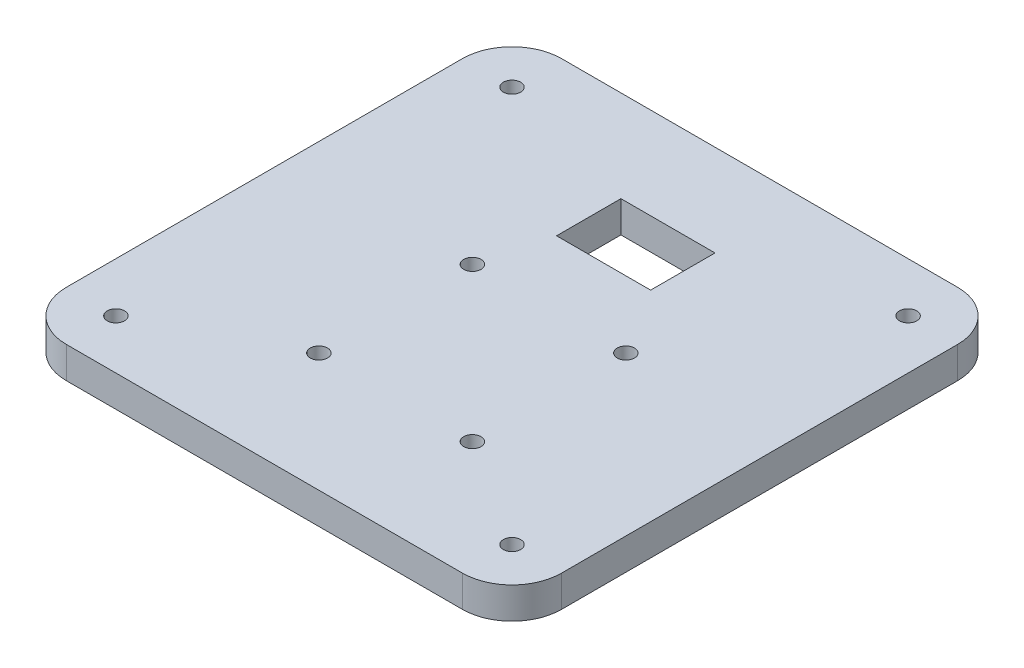
SolidWorks part; units mm, degrees
ref_plane "Front Plane" through (0, 0, 0) normal (0, 0, 1) x (1, 0, 0)
ref_plane "Top Plane" through (0, 0, 0) normal (0, 1, 0) x (1, 0, 0)
ref_plane "Right Plane" through (0, 0, 0) normal (1, 0, 0) x (0, 0, -1)
sketch "Sketch2" plane through (0, 0, 0) normal (0, 1, 0) x (1, 0, 0)
  line L1 (-50, 50) -> (50, 50)
  line L2 (-50, 50) -> (-50, -50)
  line L3 (-50, -50) -> (50, -50)
  line L4 (50, 50) -> (50, -50)
  line L5 (-50, 50) -> (50, -50) construction
  line L6 (-50, -50) -> (50, 50) construction
  point P0 (0, 0)
  dimension "D1" = 100
  dimension "D2" = 100
extrude "Boss-Extrude1" add sketch "Sketch2" along normal blind 6.35 contours L2 L3 L4 L1
sketch "Sketch3" plane through (0, 0, 0) normal (0, -1, 0) x (1, 0, 0)
  line L0 (-50, -50) -> (-50, 50) construction
  line L1 (-50, -50) -> (50, -50) construction
  circle A0 centre (-40, -40) radius 1.75
  dimension "D1" = 10
  dimension "D3" = 3.5
  dimension "D2" = 10
extrude "Cut-Extrude1" cut sketch "Sketch3" against normal through all
pattern_linear "LPattern1" count 2 spacing 80 along (0, 0, 1) of "Cut-Extrude1"
pattern_linear "LPattern2" count 2 spacing 80 along (1, 0, 0) of "LPattern1", "Cut-Extrude1"
sketch "Sketch8" plane through (0, 0, 0) normal (0, -1, 0) x (1, 0, 0)
  line L0 (50, -50) -> (50, 50) construction
  line L1 (-50, -50) -> (50, -50) construction
  circle A0 centre (18, -5) radius 1.75
  dimension "D1" = 32
  dimension "D3" = 3.5
  dimension "D2" = 45
extrude "Cut-Extrude2" cut sketch "Sketch8" against normal through all
pattern_linear "LPattern3" count 2 spacing 31 along (0, 0, 1) of "Cut-Extrude2"
pattern_linear "LPattern4" count 2 spacing 31 along (-1, 0, 0) of "LPattern3", "Cut-Extrude2"
sketch "Sketch9" plane through (0, 0, 0) normal (0, -1, 0) x (1, 0, 0)
  line L0 (50, -50) -> (50, 50) construction
  line L1 (-9.5, -31.5) -> (9.5, -31.5)
  line L2 (-9.5, -31.5) -> (-9.5, -18.5)
  line L3 (-9.5, -18.5) -> (9.5, -18.5)
  line L4 (9.5, -31.5) -> (9.5, -18.5)
  line L5 (-9.5, -31.5) -> (9.5, -18.5) construction
  line L6 (-9.5, -18.5) -> (9.5, -31.5) construction
  line L7 (-50, -50) -> (50, -50) construction
  point P0 (0, -25)
  dimension "D1" = 50
  dimension "D2" = 25
  dimension "D3" = 13
  dimension "D4" = 19
extrude "Cut-Extrude3" cut sketch "Sketch9" against normal through all
fillet "Fillet1" radius 10 4 edges at (-50, 3.175, 50) (50, 3.175, 50) (50, 3.175, -50) (-50, 3.175, -50)
